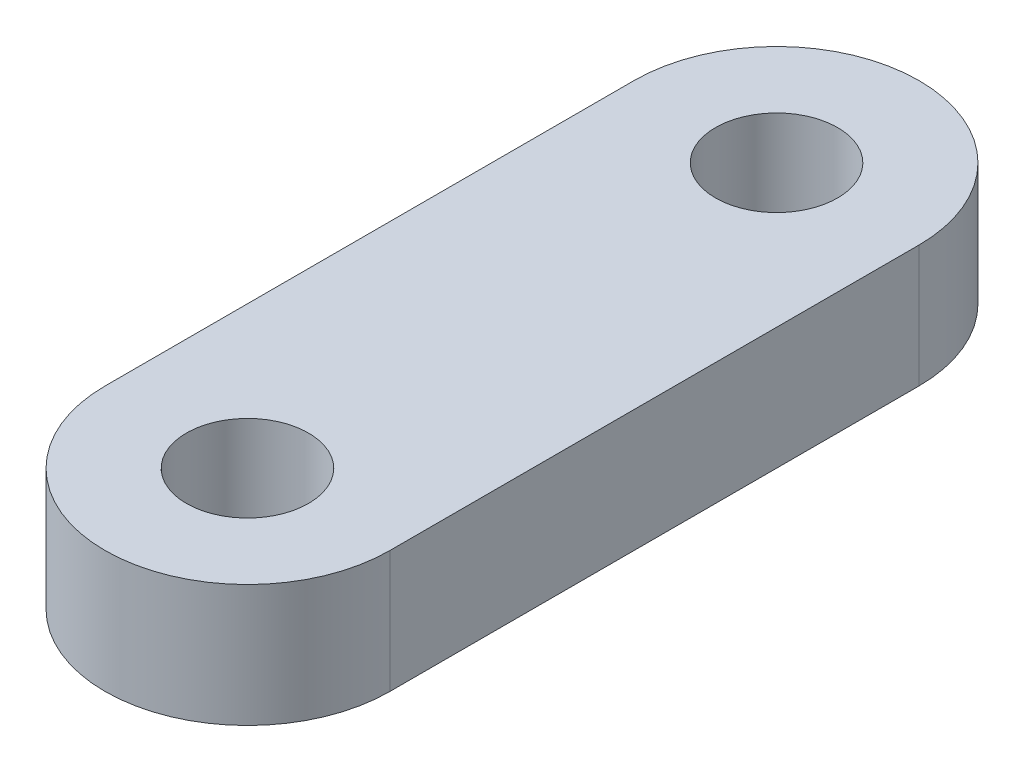
SolidWorks part; units mm, degrees
ref_plane "Plano frontal" through (0, 0, 0) normal (0, 0, 1) x (1, 0, 0)
ref_plane "Plano superior" through (0, 0, 0) normal (0, 1, 0) x (1, 0, 0)
ref_plane "Plano direito" through (0, 0, 0) normal (1, 0, 0) x (0, 0, -1)
sketch "Sketch1" plane through (0, 0, 0) normal (0, 1, 0) x (1, 0, 0)
  line L0 (0, -6.5) -> (0, 6.5) construction
  line L1 (-3.5, -6.5) -> (-3.5, 6.5)
  line L2 (3.5, -6.5) -> (3.5, 6.5)
  arc A0 (-3.5, -6.5) -> (3.5, -6.5) centre (0, -6.5) ccw
  arc A1 (3.5, 6.5) -> (-3.5, 6.5) centre (0, 6.5) ccw
  circle A2 centre (0, 6.5) radius 1.5
  circle A3 centre (0, -6.5) radius 1.5
  point P2 (0, 0)
  dimension "D1" = 3
  dimension "D2" = 2
  dimension "D3" = 13
extrude "Boss-Extrude1" add sketch "Sketch1" along normal mid plane 3
